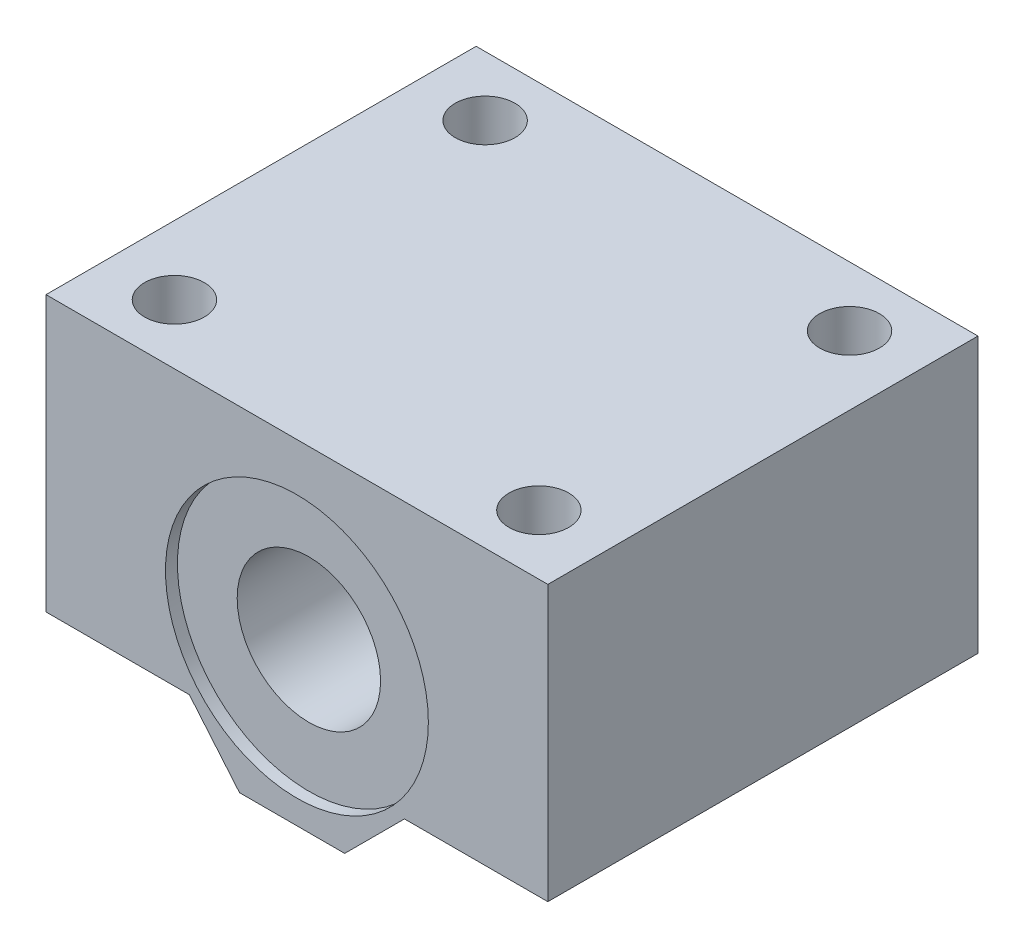
SolidWorks part; units mm, degrees
ref_plane "Front Plane" through (0, 0, 0) normal (0, 0, 1) x (1, 0, 0)
ref_plane "Top Plane" through (0, 0, 0) normal (0, 1, 0) x (1, 0, 0)
ref_plane "Right Plane" through (0, 0, 0) normal (1, 0, 0) x (0, 0, -1)
sketch "Sketch1" plane through (0, 0, 0) normal (0, 0, 1) x (1, 0, 0)
  line L1 (-21, -14) -> (21, -14)
  line L2 (-21, -14) -> (-21, 14)
  line L3 (-21, 14) -> (21, 14)
  line L4 (21, -14) -> (21, 14)
  line L5 (-21, -14) -> (21, 14) construction
  line L6 (-21, 14) -> (21, -14) construction
  circle A0 centre (0, -1) radius 6
  point P0 (0, 0)
  dimension "D3" = 12
  dimension "D1" = 42
  dimension "D2" = 28
  dimension "D4" = 21
  dimension "D5" = 15
extrude "Boss-Extrude1" add sketch "Sketch1" along normal mid plane 36
sketch "Sketch6" plane through (0, 0, 18) normal (0, 0, 1) x (1, 0, 0)
  line L1 (-21, 14) -> (-21, -14) construction
  line L7 (21, -14) -> (21, 14) construction
  line L11 (-21, -9) -> (-9, -9)
  line L12 (-9, -9) -> (-4.8045, -14)
  line L13 (-21, -14) -> (21, -14) construction
  line L14 (-4.8045, -14) -> (-21, -14)
  line L15 (-21, -14) -> (-21, -9)
  line L16 (21, -9) -> (9, -9)
  line L17 (9, -9) -> (4, -14)
  line L18 (4, -14) -> (21, -14)
  line L19 (21, -14) -> (21, -9)
  dimension "D6" = 12
  dimension "D7" = 135
  dimension "D8" = 5
  dimension "D9" = 130
  dimension "D10" = 12
extrude "Cut-Extrude5" cut sketch "Sketch6" against normal through all
sketch "Sketch2" plane through (0, 14, 0) normal (0, -1, 0) x (-1, 0, 0)
  line L0 (0, -18) -> (0, 18) construction
  line L3 (21, 0) -> (-21, 0) construction
  circle A0 centre (15.25, -13) radius 2.15
  circle A1 centre (-15.25, -13) radius 2.15
  circle A2 centre (-15.25, 13) radius 2.15
  circle A3 centre (15.25, 13) radius 2.15
  dimension "D1" = 4.3
  dimension "D2" = 4.3
  dimension "D3" = 4.3
  dimension "D4" = 4.3
  dimension "D5" = 15.25
  dimension "D6" = 15.25
  dimension "D7" = 15.25
  dimension "D8" = 15.25
  dimension "D9" = 13
  dimension "D10" = 13
  dimension "D11" = 13
  dimension "D12" = 13
extrude "Cut-Extrude1" cut sketch "Sketch2" along normal through all
sketch "Sketch3" plane through (0, 14, 0) normal (0, -1, 0) x (1, 0, 0)
  circle A0 centre (-15.25, 13) radius 2.5
  circle A1 centre (15.25, 13) radius 2.5
  circle A2 centre (15.25, -13) radius 2.5
  circle A3 centre (-15.25, -13) radius 2.5
  dimension "D1" = 5
  dimension "D2" = 5
  dimension "D3" = 5
  dimension "D4" = 5
extrude "Cut-Extrude2" cut sketch "Sketch3" along normal blind 12
sketch "Sketch4" plane through (0, 0, 18) normal (0, 0, 1) x (1, 0, 0)
  circle A0 centre (0, -1) radius 11
  dimension "D1" = 22
extrude "Cut-Extrude3" cut sketch "Sketch4" against normal blind 1
sketch "Sketch5" plane through (0, 0, -18) normal (0, 0, -1) x (-1, 0, 0)
  circle A0 centre (0, -1) radius 11
  dimension "D1" = 22
extrude "Cut-Extrude4" cut sketch "Sketch5" against normal blind 1
